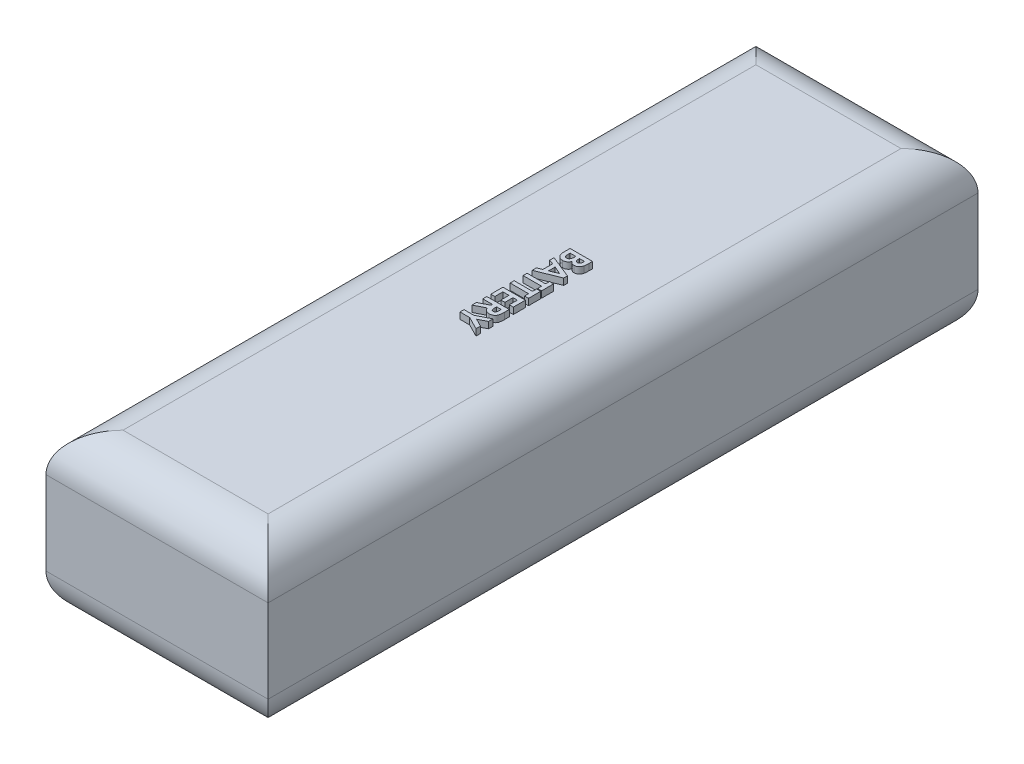
SolidWorks part; units mm, degrees
ref_plane "Front Plane" through (0, 0, 0) normal (0, 0, 1) x (1, 0, 0)
ref_plane "Top Plane" through (0, 0, 0) normal (0, 1, 0) x (1, 0, 0)
ref_plane "Right Plane" through (0, 0, 0) normal (1, 0, 0) x (0, 0, -1)
sketch "Sketch1" plane through (0, 0, 0) normal (0, 1, 0) x (1, 0, 0)
  line L1 (-19.9464, 65.1875) -> (14.6536, 65.1875)
  line L2 (-19.9464, 65.1875) -> (-19.9464, -45.4125)
  line L3 (-19.9464, -45.4125) -> (14.6536, -45.4125)
  line L4 (14.6536, 65.1875) -> (14.6536, -45.4125)
  dimension "D1" = 34.6
  dimension "D2" = 110.6
extrude "Boss-Extrude1" add sketch "Sketch1" along normal blind 25
fillet "Fillet1" radius 6 8 edges at (-19.9464, 0, -9.8875) (14.6536, 0, -9.8875) (-19.9464, 25, -9.8875) (14.6536, 25, -9.8875) (-2.6464, 0, -65.1875) (-2.6464, 25, -65.1875) (-2.6464, 0, 45.4125) (-2.6464, 25, 45.4125)
sketch "Sketch2" plane through (0, 25, 0) normal (0, 1, 0) x (1, 0, 0)
  line L0 (-2.6464, 59.1875) -> (-2.6464, -39.4125) construction
  line L1 (8.6536, 59.1875) -> (-13.9464, 59.1875) construction
  line L2 (-13.9464, -39.4125) -> (8.6536, -39.4125) construction
  text T0 "<b>BATTERY</b>"
extrude "Boss-Extrude2" add sketch "Sketch2" along normal blind 1
